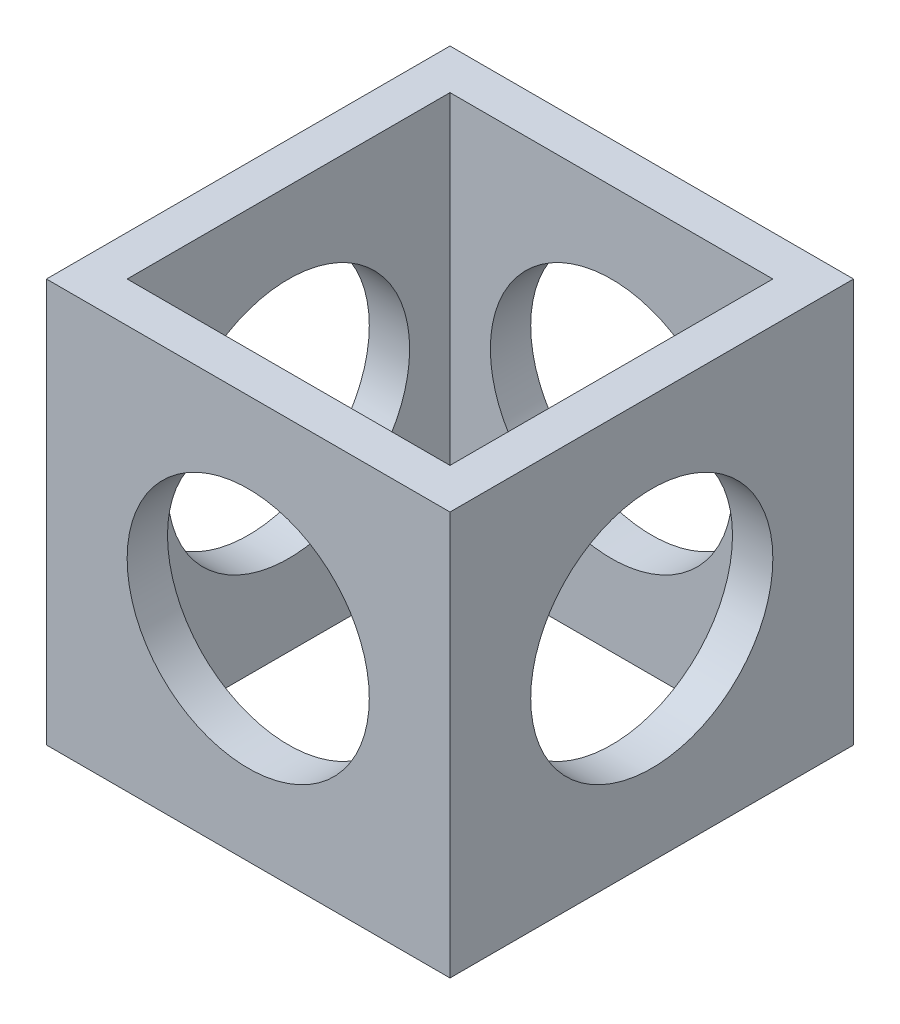
SolidWorks part; units mm, degrees
ref_plane "Alzado" through (0, 0, 0) normal (0, 0, 1) x (1, 0, 0)
ref_plane "Planta" through (0, 0, 0) normal (0, 1, 0) x (1, 0, 0)
ref_plane "Vista lateral" through (0, 0, 0) normal (1, 0, 0) x (0, 0, -1)
sketch "Croquis1" plane through (0, 0, 0) normal (0, 1, 0) x (1, 0, 0)
  line L0 (20, 20) -> (20, -20)
  line L1 (-25, 25) -> (25, 25)
  line L2 (-25, 25) -> (-25, -25)
  line L3 (-25, -25) -> (25, -25)
  line L4 (25, 25) -> (25, -25)
  line L5 (-25, 25) -> (25, -25) construction
  line L6 (-25, -25) -> (25, 25) construction
  line L7 (-20, -20) -> (20, -20)
  line L8 (-20, 20) -> (-20, -20)
  line L9 (-20, 20) -> (20, 20)
  point P0 (0, 0)
  dimension "D1" = 50
  dimension "D2" = 50
  dimension "D3" = 5
extrude "Saliente-Extruir1" add sketch "Croquis1" along normal blind 50
sketch "Croquis2" plane through (25, 0, 0) normal (1, 0, 0) x (0, 0, -1)
  circle A0 centre (0, 25) radius 15
  dimension "D1" = 30
extrude "Cortar-Extruir1" cut sketch "Croquis2" against normal blind 50
sketch "Croquis3" plane through (0, 0, -25) normal (0, 0, -1) x (-1, 0, 0)
  circle A0 centre (0, 25) radius 15
  dimension "D1" = 30
extrude "Cortar-Extruir2" cut sketch "Croquis3" against normal blind 50
